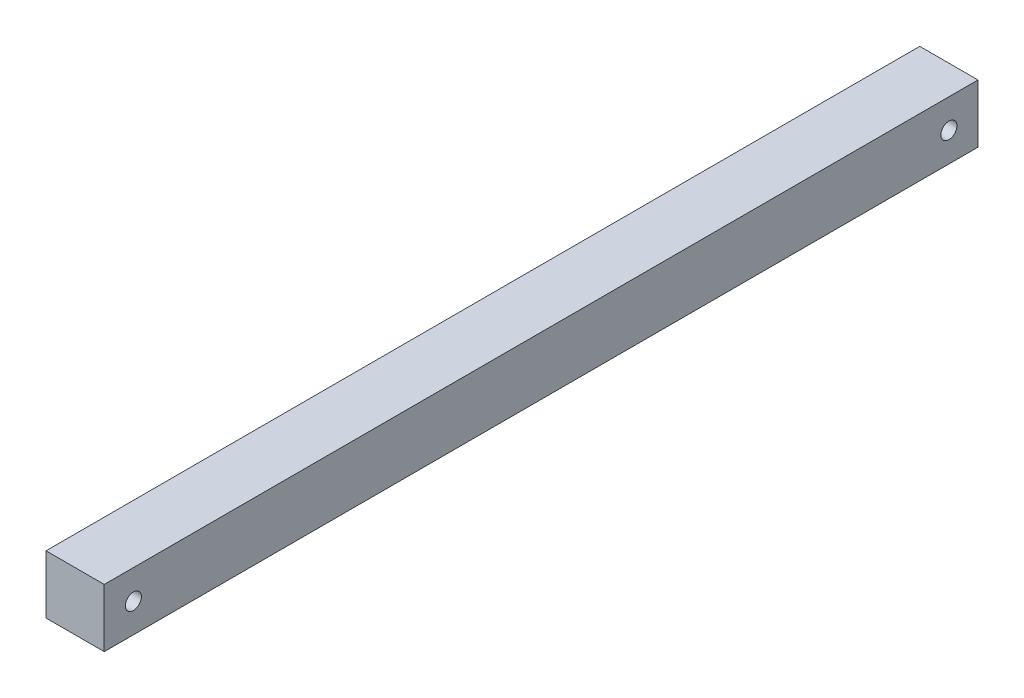
SolidWorks part; units mm, degrees
ref_plane "Front Plane" through (0, 0, 0) normal (0, 0, 1) x (1, 0, 0)
ref_plane "Top Plane" through (0, 0, 0) normal (0, 1, 0) x (1, 0, 0)
ref_plane "Right Plane" through (0, 0, 0) normal (1, 0, 0) x (0, 0, -1)
sketch "Sketch1" plane through (0, 0, 0) normal (0, 0, 1) x (1, 0, 0)
  line L5 (-12.7, -12.7) -> (12.7, -12.7)
  line L6 (-12.7, -12.7) -> (-12.7, 12.7)
  line L7 (-12.7, 12.7) -> (12.7, 12.7)
  line L8 (12.7, -12.7) -> (12.7, 12.7)
  line L9 (-12.7, -12.7) -> (12.7, 12.7) construction
  line L10 (-12.7, 12.7) -> (12.7, -12.7) construction
  point P0 (0, 0)
  dimension "D1" = 25.4
  dimension "D2" = 25.4
extrude "Boss-Extrude1" add sketch "Sketch1" along normal blind 381
sketch "Sketch10" plane through (-12.7, 0, 0) normal (-1, 0, 0) x (0, 0, 1)
  line L0 (190.5, 12.7) -> (190.5, 75.2381) construction
  line L1 (381, 12.7) -> (0, 12.7) construction
  line L2 (381, 12.7) -> (381, -12.7) construction
  circle A0 centre (368.3, 0) radius 3.5
  circle A1 centre (12.7, 0) radius 3.5
  dimension "D1" = 7
  dimension "D3" = 12.7
  dimension "D2" = 12.7
extrude "Cut-Extrude6" cut sketch "Sketch10" against normal through all
